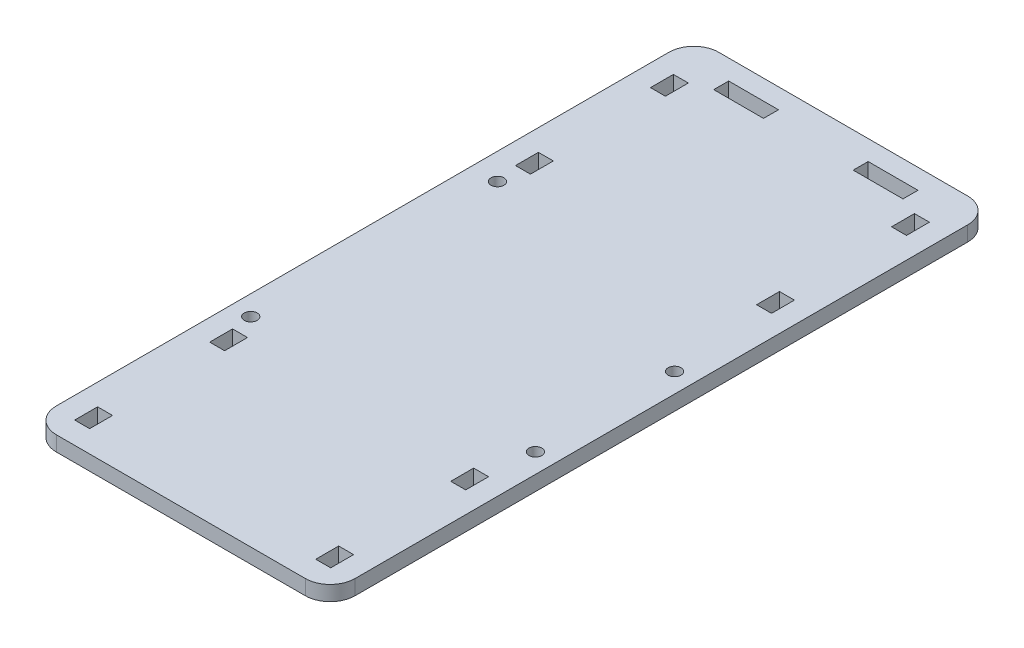
SolidWorks part; units mm, degrees
ref_plane "Front Plane" through (0, 0, 0) normal (0, 0, 1) x (1, 0, 0)
ref_plane "Top Plane" through (0, 0, 0) normal (0, 1, 0) x (1, 0, 0)
ref_plane "Right Plane" through (0, 0, 0) normal (1, 0, 0) x (0, 0, -1)
sketch "Sketch1" plane through (0, 0, 0) normal (0, 1, 0) x (1, 0, 0)
  line L0 (11, 101) -> (11, 104)
  line L2 (0, -20) -> (0, 103)
  line L4 (60, -20) -> (60, 103)
  line L5 (11, 104) -> (21, 104)
  line L6 (21, 104) -> (21, 101)
  line L8 (39, 101) -> (39, 104)
  line L9 (39, 104) -> (49, 104)
  line L10 (49, 104) -> (49, 101)
  line L13 (0, 41.5) -> (60, 41.5) construction
  line L15 (7.3, 95) -> (4.3, 95)
  line L16 (7.3, 95) -> (7.3, 99.6)
  line L17 (7.3, 99.6) -> (4.3, 99.6)
  line L18 (4.3, 95) -> (4.3, 99.6)
  line L19 (30, 108) -> (30, -25) construction
  line L22 (7.3, 72.5) -> (4.3, 72.5)
  line L23 (7.3, 72.5) -> (7.3, 67.9)
  line L24 (7.3, 67.9) -> (4.3, 67.9)
  line L25 (4.3, 72.5) -> (4.3, 67.9)
  line L26 (11, 101) -> (21, 101)
  line L29 (52.7, 72.5) -> (52.7, 67.9)
  line L30 (52.7, 67.9) -> (55.7, 67.9)
  line L31 (55.7, 72.5) -> (55.7, 67.9)
  line L32 (52.7, 72.5) -> (55.7, 72.5)
  line L33 (52.7, 95) -> (55.7, 95)
  line L34 (52.7, 95) -> (52.7, 99.6)
  line L35 (55.7, 95) -> (55.7, 99.6)
  line L36 (52.7, 99.6) -> (55.7, 99.6)
  line L38 (7.3, 11.1) -> (4.3, 11.1)
  line L39 (7.3, 6.5) -> (7.3, 11.1)
  line L40 (4.3, 6.5) -> (4.3, 11.1)
  line L41 (7.3, 6.5) -> (4.3, 6.5)
  line L42 (7.3, -16) -> (4.3, -16)
  line L43 (7.3, -16) -> (7.3, -20.6)
  line L44 (4.3, -16) -> (4.3, -20.6)
  line L45 (7.3, -20.6) -> (4.3, -20.6)
  line L46 (55.7, 6.5) -> (55.7, 11.1)
  line L47 (52.7, 6.5) -> (55.7, 6.5)
  line L48 (52.7, 6.5) -> (52.7, 11.1)
  line L49 (52.7, 11.1) -> (55.7, 11.1)
  line L50 (55.7, -16) -> (55.7, -20.6)
  line L51 (52.7, -16) -> (55.7, -16)
  line L52 (52.7, -16) -> (52.7, -20.6)
  line L53 (52.7, -20.6) -> (55.7, -20.6)
  line L54 (39, 101) -> (49, 101)
  line L55 (5, 108) -> (55, 108)
  line L56 (5, -25) -> (55, -25)
  arc A2 (55, -25) -> (60, -20) centre (55, -20) ccw
  arc A3 (5, -25) -> (0, -20) centre (5, -20) cw
  arc A4 (60, 103) -> (55, 108) centre (55, 103) ccw
  arc A5 (0, 103) -> (5, 108) centre (5, 103) cw
  circle A7 centre (56.07, 48.0689) radius 1.3
  circle A8 centre (4, 15.0489) radius 1.3
  circle A9 centre (56.07, 20.1289) radius 1.3
  circle A10 centre (5.27, 63.3089) radius 1.3
  point P4 (60, -25)
  point P22 (0, -25)
  point P34 (39, 102.5)
  dimension "D2" = 5
  dimension "D3" = 18
  dimension "D4" = 60
  dimension "D5" = 9
  dimension "D1" = 4
  dimension "D6" = 4.3
  dimension "D7" = 4.3
  dimension "D8" = 3
  dimension "D9" = 3
  dimension "D10" = 4.6
  dimension "D11" = 4.6
  dimension "D12" = 4.6
  dimension "D13" = 4.6
  dimension "D14" = 3
  dimension "D15" = 3
extrude "Boss-Extrude1" add sketch "Sketch1" along normal blind 3
